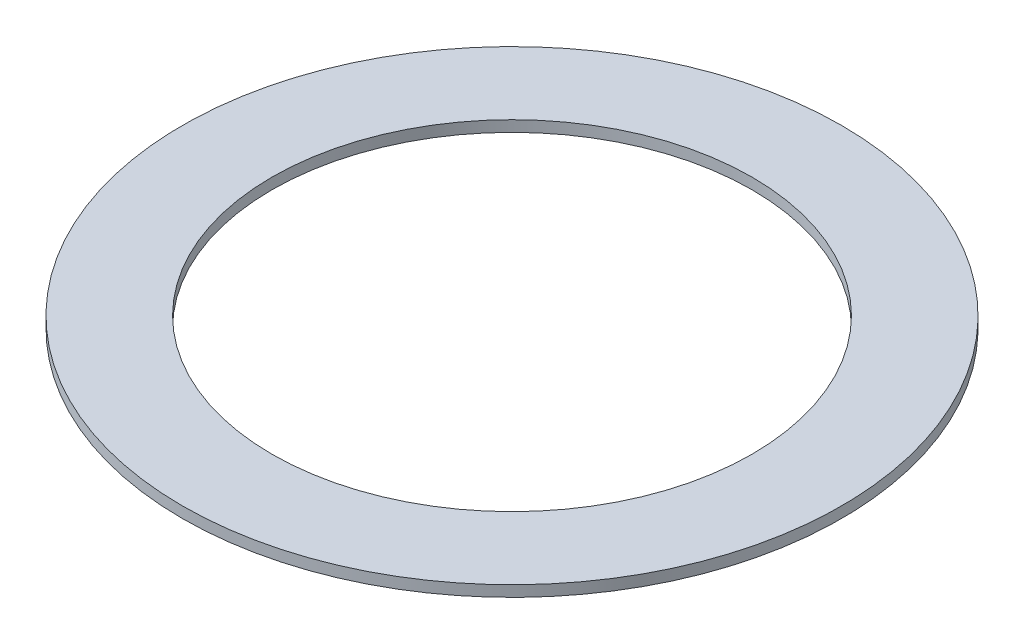
SolidWorks part; units mm, degrees
ref_plane "Front Plane" through (0, 0, 0) normal (0, 0, 1) x (1, 0, 0)
ref_plane "Top Plane" through (0, 0, 0) normal (0, 1, 0) x (1, 0, 0)
ref_plane "Right Plane" through (0, 0, 0) normal (1, 0, 0) x (0, 0, -1)
sketch "Sketch1" plane through (0, 0, 0) normal (0, 1, 0) x (1, 0, 0)
  circle A0 centre (0, 0) radius 30
  circle A1 centre (0, 0) radius 21.85
  dimension "D1" = 60
  dimension "D2" = 43.7
extrude "Boss-Extrude1" add sketch "Sketch1" along normal blind 1
